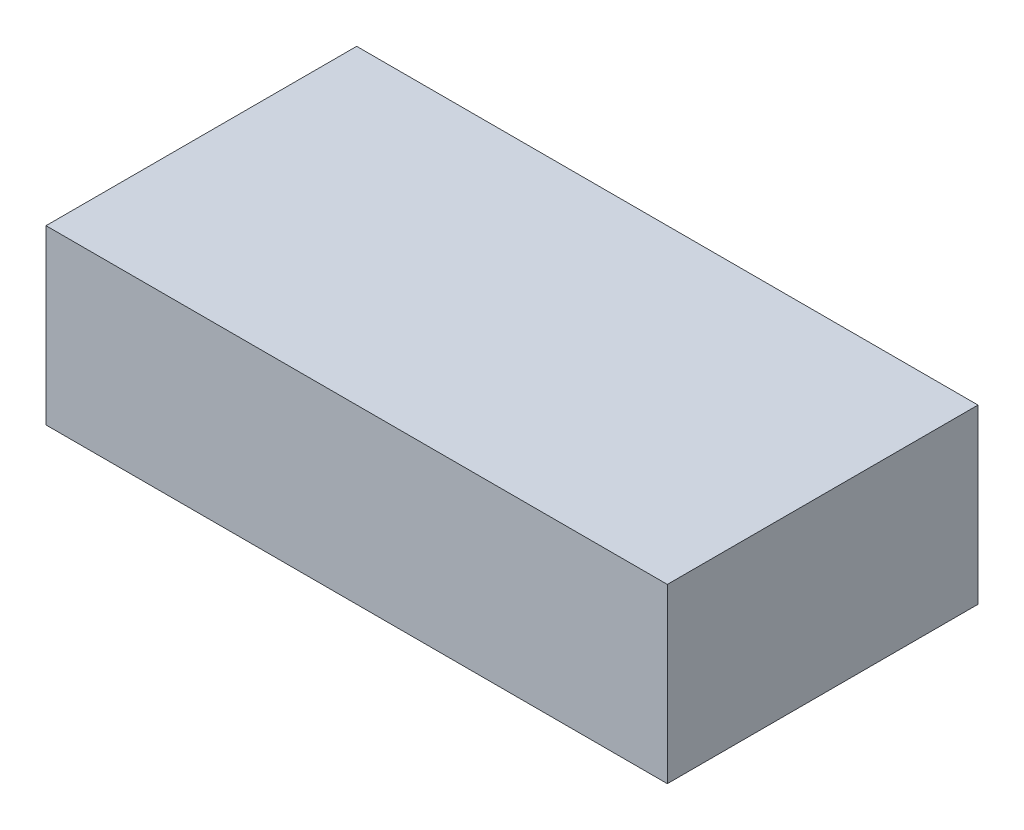
SolidWorks part; units mm, degrees
ref_plane "Front Plane" through (0, 0, 0) normal (0, 0, 1) x (1, 0, 0)
ref_plane "Top Plane" through (0, 0, 0) normal (0, 1, 0) x (1, 0, 0)
ref_plane "Right Plane" through (0, 0, 0) normal (1, 0, 0) x (0, 0, -1)
sketch "Sketch1" plane through (0, 0, 0) normal (0, 1, 0) x (1, 0, 0)
  line L1 (-114.3, -57.15) -> (114.3, -57.15)
  line L2 (-114.3, -57.15) -> (-114.3, 57.15)
  line L3 (-114.3, 57.15) -> (114.3, 57.15)
  line L4 (114.3, -57.15) -> (114.3, 57.15)
  line L5 (-114.3, -57.15) -> (114.3, 57.15) construction
  line L6 (-114.3, 57.15) -> (114.3, -57.15) construction
  point P0 (0, 0)
  dimension "D1" = 228.6
  dimension "D2" = 114.3
extrude "Boss-Extrude1" add sketch "Sketch1" along normal blind 63.5 contours L3 L4 L1 L2
sketch "Sketch2" plane through (-114.3, 0, 0) normal (-1, 0, 0) x (0, 0, 1)
  line L0 (-38.1, 57.15) -> (38.1, 57.15) construction
  line L1 (57.15, 63.5) -> (-57.15, 63.5) construction
  circle A0 centre (-38.1, 57.15) radius 1.5875
  circle A1 centre (38.1, 57.15) radius 1.5875
  point P4 (0, 0)
  point P5 (0, 0)
  point P7 (0, 57.15)
  dimension "D1" = 3.175
  dimension "D2" = 6.35
  dimension "D3" = 76.2
extrude "Cut-Extrude1" cut sketch "Sketch2" against normal blind 6.35
